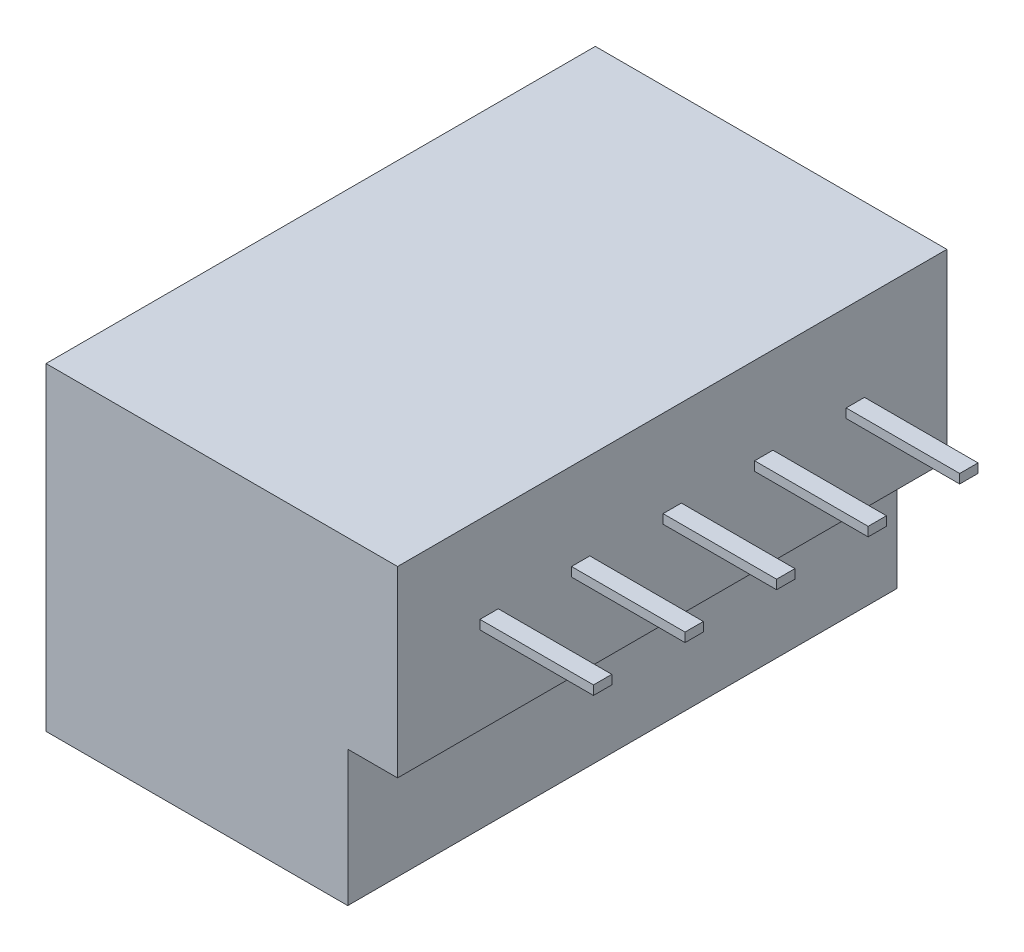
SolidWorks part; units mm, degrees
ref_plane "Front Plane" through (0, 0, 0) normal (0, 0, 1) x (1, 0, 0)
ref_plane "Top Plane" through (0, 0, 0) normal (0, 1, 0) x (1, 0, 0)
ref_plane "Right Plane" through (0, 0, 0) normal (1, 0, 0) x (0, 0, -1)
sketch "Sketch1" plane through (0, 0, 0) normal (0, 1, 0) x (1, 0, 0)
  line L1 (-20.3569, 6.7781) -> (-12.1169, 6.7781)
  line L2 (-20.3569, 6.7781) -> (-20.3569, -8.2219)
  line L3 (-20.3569, -8.2219) -> (-12.1169, -8.2219)
  line L4 (-12.1169, 6.7781) -> (-12.1169, -8.2219)
  dimension "D1" = 15
  dimension "D2" = 8.24
extrude "Boss-Extrude1" add sketch "Sketch1" along normal blind 3.7
sketch "Sketch2" plane through (0, 3.7, 0) normal (0, 1, 0) x (1, 0, 0)
  line L1 (-20.3569, -8.2219) -> (-12.1169, -8.2219)
  line L2 (-20.3569, -8.2219) -> (-20.3569, 6.7781)
  line L3 (-20.3569, 6.7781) -> (-12.1169, 6.7781)
  line L5 (-12.1169, 6.7781) -> (-10.7569, 6.7781)
  line L7 (-12.1169, -8.2219) -> (-10.7569, -8.2219)
  line L8 (-10.7569, 6.7781) -> (-10.7569, -8.2219)
  dimension "D1" = 1.36
extrude "Boss-Extrude2" add sketch "Sketch2" along normal blind 5
sketch "Sketch3" plane through (-10.7569, 0, 0) normal (1, 0, 0) x (0, 0, -1)
  line L0 (-8.2219, 8.7) -> (6.7781, 8.7) construction
  line L1 (-5.9719, 6.325) -> (-5.4719, 6.325)
  line L2 (-5.9719, 6.325) -> (-5.9719, 6.075)
  line L3 (-5.9719, 6.075) -> (-5.4719, 6.075)
  line L4 (-5.4719, 6.325) -> (-5.4719, 6.075)
  line L5 (-8.2219, 3.7) -> (6.7781, 3.7) construction
  line L6 (6.7781, 8.7) -> (6.7781, 3.7) construction
  line L7 (-3.4719, 6.325) -> (-2.9719, 6.325)
  line L8 (-3.4719, 6.325) -> (-3.4719, 6.075)
  line L9 (-3.4719, 6.075) -> (-2.9719, 6.075)
  line L10 (-2.9719, 6.325) -> (-2.9719, 6.075)
  line L11 (-0.9719, 6.325) -> (-0.4719, 6.325)
  line L12 (-0.9719, 6.325) -> (-0.9719, 6.075)
  line L13 (-0.9719, 6.075) -> (-0.4719, 6.075)
  line L14 (-0.4719, 6.325) -> (-0.4719, 6.075)
  line L15 (1.5281, 6.325) -> (2.0281, 6.325)
  line L16 (1.5281, 6.325) -> (1.5281, 6.075)
  line L17 (1.5281, 6.075) -> (2.0281, 6.075)
  line L18 (2.0281, 6.325) -> (2.0281, 6.075)
  line L19 (4.0281, 6.325) -> (4.5281, 6.325)
  line L20 (4.0281, 6.325) -> (4.0281, 6.075)
  line L21 (4.0281, 6.075) -> (4.5281, 6.075)
  line L22 (4.5281, 6.325) -> (4.5281, 6.075)
  line L23 (-8.2219, 8.7) -> (-8.2219, 3.7) construction
  dimension "D1" = 0.5
  dimension "D2" = 0.25
  dimension "D3" = 2.375
  dimension "D4" = 2.375
  dimension "D5" = 0.5
  dimension "D6" = 0.5
  dimension "D7" = 0.5
  dimension "D8" = 0.5
  dimension "D9" = 2.25
  dimension "D10" = 2
  dimension "D11" = 2
  dimension "D12" = 2
  dimension "D13" = 2.25
extrude "Boss-Extrude3" add sketch "Sketch3" along normal blind 3.1
sketch "Sketch4" plane through (0, 0, 0) normal (0, -1, 0) x (-1, 0, 0)
  line L0 (20.3569, 6.7781) -> (20.3569, -8.2219) construction
  line L1 (12.1169, -8.2219) -> (12.1169, 6.7781) construction
  line L2 (20.3569, -8.2219) -> (12.1169, -8.2219) construction
  line L3 (12.1169, 6.7781) -> (20.3569, 6.7781) construction
  circle A0 centre (16.2369, -4.7219) radius 2.25
  circle A1 centre (16.2369, 3.2781) radius 2
  point P8 (16.2369, -8.2219)
  point P11 (16.2369, 6.7781)
  dimension "D1" = 4.5
  dimension "D2" = 4
  dimension "D3" = 4.12
  dimension "D4" = 4.12
  dimension "D5" = 4.12
  dimension "D6" = 8
  dimension "D7" = 3.5
  dimension "D8" = 3.5
extrude "Cut-Extrude1" cut sketch "Sketch4" against normal blind 0.5
